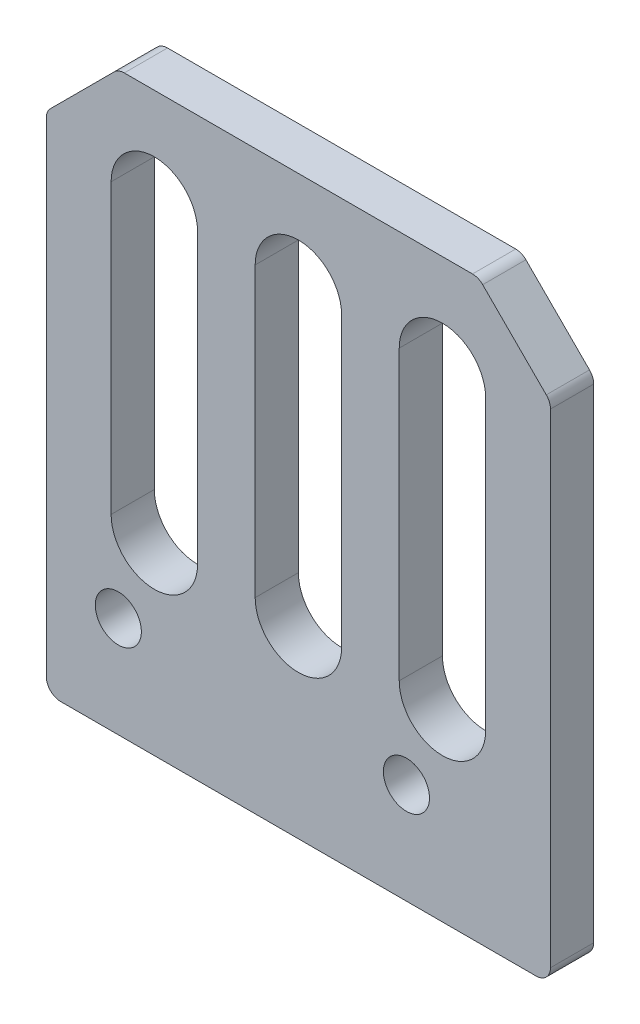
SolidWorks part; units mm, degrees
material "Thornel Mat VMA"
ref_plane "前视基准面" through (0, 0, 0) normal (0, 0, 1) x (1, 0, 0)
ref_plane "上视基准面" through (0, 0, 0) normal (0, 1, 0) x (1, 0, 0)
ref_plane "右视基准面" through (0, 0, 0) normal (1, 0, 0) x (0, 0, -1)
sketch "草图1" plane through (0, 0, 0) normal (0, 0, 1) x (1, 0, 0)
  line L1 (-17.5, 20) -> (17.5, 20)
  line L2 (-17.5, 20) -> (-17.5, -20)
  line L3 (-17.5, -20) -> (17.5, -20)
  line L4 (17.5, 20) -> (17.5, -20)
  line L5 (-17.5, 20) -> (17.5, -20) construction
  line L6 (-17.5, -20) -> (17.5, 20) construction
  point P0 (0, 0)
  dimension "D1" = 35
  dimension "D2" = 40
extrude "凸台-拉伸1" add sketch "草图1" along normal blind 3
chamfer "倒角1" distance 5 angle 45 2 edges at (-17.5, 20, 1.5) (17.5, 20, 1.5)
fillet "圆角1" radius 1 6 edges at (12.5, 20, 1.5) (17.5, 15, 1.5) (17.5, -20, 1.5) (-17.5, 15, 1.5) (-12.5, 20, 1.5) (-17.5, -20, 1.5)
sketch "草图2" plane through (0, 0, 3) normal (0, 0, 1) x (1, 0, 0)
  line L0 (-12.5, -13) -> (7.5, -13) construction
  line L1 (-16.5, -20) -> (16.5, -20) construction
  line L2 (-17.5, 14.5858) -> (-17.5, -19) construction
  circle A0 centre (-12.5, -13) radius 1.6
  circle A1 centre (7.5, -13) radius 1.6
  dimension "D4" = 3.2
  dimension "D1" = 7
  dimension "D2" = 5
  dimension "D3" = 20
extrude "切除-拉伸1" cut sketch "草图2" against normal through all
sketch "草图3" plane through (0, 0, 3) normal (0, 0, 1) x (1, 0, 0)
  line L0 (0, 13) -> (0, -7) construction
  line L1 (3, 13) -> (3, -7)
  line L2 (-3, 13) -> (-3, -7)
  line L3 (-10, 13) -> (-10, -7) construction
  line L4 (-7, 13) -> (-7, -7)
  line L5 (-13, 13) -> (-13, -7)
  line L6 (10, 13) -> (10, -7) construction
  line L7 (13, 13) -> (13, -7)
  line L8 (7, 13) -> (7, -7)
  arc A0 (3, 13) -> (-3, 13) centre (0, 13) ccw
  arc A1 (-3, -7) -> (3, -7) centre (0, -7) ccw
  arc A2 (-7, 13) -> (-13, 13) centre (-10, 13) ccw
  arc A3 (-13, -7) -> (-7, -7) centre (-10, -7) ccw
  arc A4 (13, 13) -> (7, 13) centre (10, 13) ccw
  arc A5 (7, -7) -> (13, -7) centre (10, -7) ccw
  point P3 (0, 3)
  point P8 (-10, 3)
  point P15 (10, 3)
  dimension "D3" = 3
  dimension "D1" = 3
  dimension "D2" = 20
  dimension "D4" = 10
  dimension "D5" = 10
extrude "切除-拉伸2" cut sketch "草图3" against normal through all
